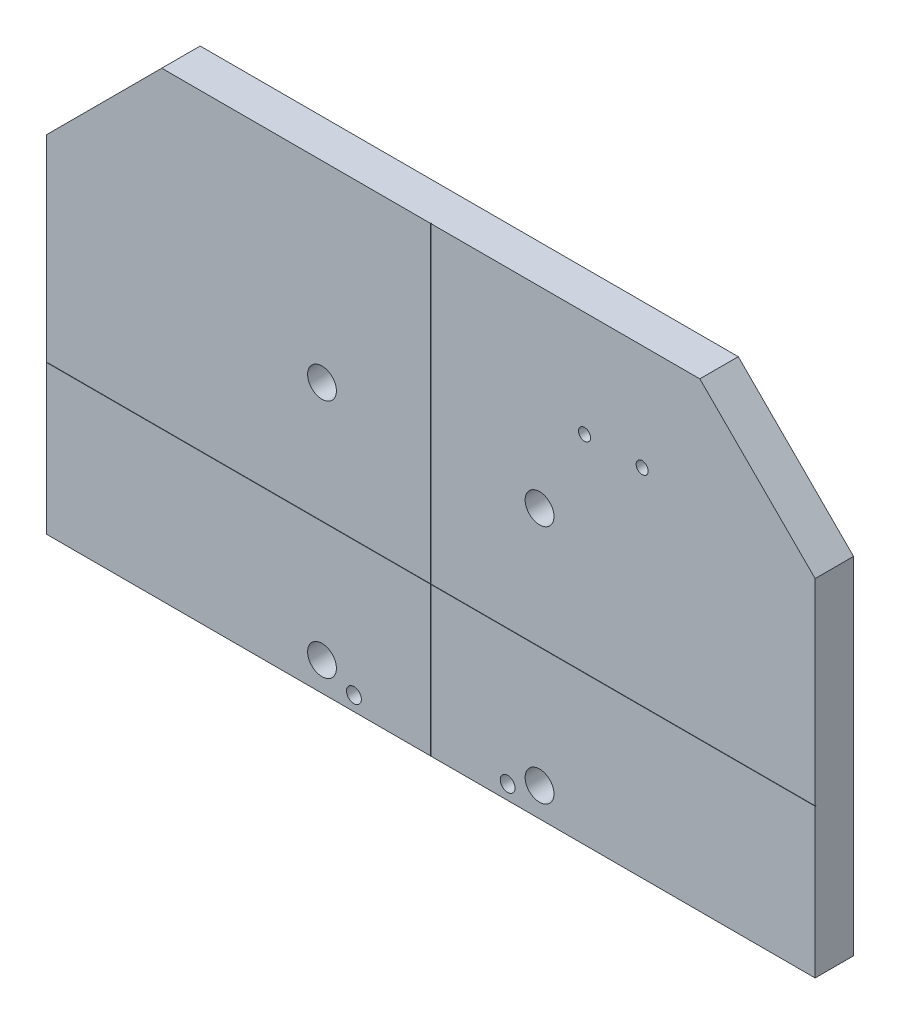
SolidWorks part; units mm, degrees
ref_plane "Front Plane" through (0, 0, 0) normal (0, 0, 1) x (1, 0, 0)
ref_plane "Top Plane" through (0, 0, 0) normal (0, 1, 0) x (1, 0, 0)
ref_plane "Right Plane" through (0, 0, 0) normal (1, 0, 0) x (0, 0, -1)
sketch "Sketch1" plane through (0, 0, 0) normal (0, 0, 1) x (1, 0, 0)
  line L0 (-281.2382, 20.8046) -> (-281.2382, -207.7954)
  line L1 (-281.2382, -207.7954) -> (226.7618, -207.7954)
  line L2 (226.7618, -207.7954) -> (226.7618, 20.8046)
  line L3 (226.7618, 20.8046) -> (150.5618, 97.0046)
  line L4 (150.5618, 97.0046) -> (-205.0382, 97.0046)
  line L5 (-205.0382, 97.0046) -> (-281.2382, 20.8046)
  dimension "D1" = 228.6
  dimension "D2" = 508
  dimension "D3" = 76.2
  dimension "D4" = 76.2
  dimension "D5" = 431.8
  dimension "D6" = 76.2
extrude "Boss-Extrude1" add sketch "Sketch1" along normal blind 25.4
sketch "Sketch2" plane through (0, 97.0046, 0) normal (0, 1, 0) x (1, 0, 0)
  line L0 (150.5618, -25.4) -> (-205.0382, -25.4) construction
  line L1 (-27.3652, -25.4) -> (-27.1112, -25.4)
  spline S0 degree 2 poles (-27.3652, -25.4) (-27.2382, -23.876) (-27.1112, -25.4) knots 0 0 0 1 1 1
  point P0 (-27.1112, -25.4)
  point P1 (-27.3652, -25.4)
  point P4 (-27.2382, -25.4)
  dimension "D1" = 0.127
  dimension "D2" = 0.127
  dimension "D3" = 0.762
extrude "Cut-Extrude1" cut sketch "Sketch2" against normal through all
sketch "Sketch3" plane through (226.7618, 0, 0) normal (1, 0, 0) x (0, 0, -1)
  line L0 (-25.4, -207.7954) -> (-25.4, 20.8046) construction
  line L1 (-25.4, -109.2434) -> (-25.4, -109.4974)
  spline S0 degree 2 poles (-25.4, -109.2434) (-23.876, -109.3704) (-25.4, -109.4974) knots 0 0 0 1 1 1
  point P0 (-25.4, -109.2434)
  point P1 (-25.4, -109.4974)
  point P7 (-25.4, -109.3704)
  dimension "D1" = 98.298
  dimension "D2" = 98.552
  dimension "D3" = 0.762
extrude "Cut-Extrude2" cut sketch "Sketch3" against normal through all
sketch "Sketch4" plane through (0, 0, 0) normal (0, 0, 1) x (1, 0, 0)
  line L0 (-281.2382, -109.4974) -> (-281.2382, -207.7954) construction
  line L1 (-281.2382, -207.7954) -> (-27.3652, -207.7954) construction
  line L2 (-27.1112, -207.7954) -> (226.7618, -207.7954) construction
  line L3 (-281.2382, 20.8046) -> (-281.2382, -109.2434) construction
  circle A0 centre (74.3618, 27.1546) radius 3.9751
  circle A1 centre (112.4618, 27.1546) radius 3.9751
  circle A2 centre (23.5618, -198.2704) radius 4.9022
  circle A3 centre (-78.0382, -198.2704) radius 4.9022
  dimension "D1" = 7.9502
  dimension "D2" = 7.9502
  dimension "D3" = 9.8044
  dimension "D4" = 9.8044
  dimension "D5" = 203.2
  dimension "D6" = 304.8
  dimension "D7" = 9.525
  dimension "D8" = 9.525
  dimension "D9" = 355.6
  dimension "D10" = 393.7
  dimension "D11" = 234.95
  dimension "D12" = 234.95
extrude "Cut-Extrude5" cut sketch "Sketch4" against normal blind 25.4 and the other way through all
sketch "Sketch6" plane through (0, 0, 0) normal (0, 0, -1) x (-1, 0, 0)
  line L1 (99.1202, -29.9954) -> (-44.6438, -29.9954)
  line L2 (99.1202, -29.9954) -> (99.1202, -188.7454)
  line L3 (99.1202, -188.7454) -> (-44.6438, -188.7454)
  line L4 (-44.6438, -29.9954) -> (-44.6438, -188.7454)
  line L5 (99.1202, -29.9954) -> (-44.6438, -188.7454) construction
  line L6 (99.1202, -188.7454) -> (-44.6438, -29.9954) construction
  point P0 (27.2382, -109.3704)
  dimension "D1" = 143.764
  dimension "D2" = 158.75
sketch "Sketch7" plane through (0, 0, 0) normal (0, 0, -1) x (-1, 0, 0)
  circle A0 centre (99.1202, -29.9954) radius 9.525
  circle A1 centre (-44.6438, -29.9954) radius 9.525
  circle A2 centre (-44.6438, -188.7454) radius 9.525
  circle A3 centre (99.1202, -188.7454) radius 9.525
  dimension "D1" = 19.05
  dimension "D2" = 19.05
  dimension "D3" = 19.05
  dimension "D4" = 19.05
extrude "Cut-Extrude6" cut sketch "Sketch7" against normal through all
